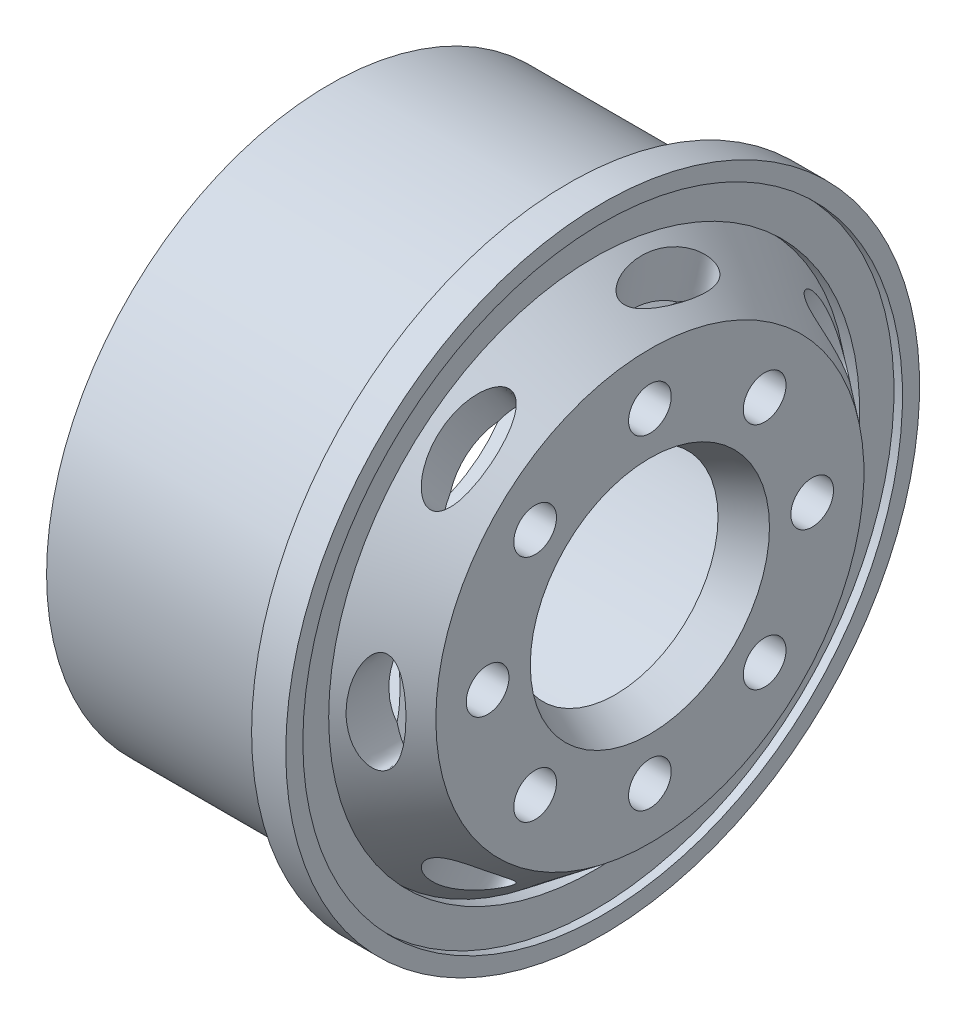
SolidWorks part; units mm, degrees
ref_plane "Front Plane" through (0, 0, 0) normal (0, 0, 1) x (1, 0, 0)
ref_plane "Top Plane" through (0, 0, 0) normal (0, 1, 0) x (1, 0, 0)
ref_plane "Right Plane" through (0, 0, 0) normal (1, 0, 0) x (0, 0, -1)
sketch "Sketch1" plane through (0, 0, 0) normal (0, 1, 0) x (1, 0, 0)
  line L0 (-37.2789, 0) -> (44.8184, 0) construction
  line L18 (5.6863, 15.538) -> (4.9553, 15.538)
  line L23 (4.9553, 15.538) -> (8.9491, 12.5285)
  line L27 (2.9431, 14.55) -> (6.9363, 11.5409)
  line L28 (4.1863, 16.55) -> (4.1863, 18.55)
  line L29 (4.1863, 18.55) -> (5.6863, 18.55)
  line L30 (5.6863, 17.55) -> (5.6863, 15.538)
  line L34 (6.9363, 11.5409) -> (6.9363, 6)
  line L37 (8.9491, 12.5285) -> (8.9491, 7)
  line L38 (6.9363, 6) -> (8.9491, 7)
  line L39 (5.6863, 18.55) -> (6.1863, 18.55)
  line L40 (6.1863, 18.55) -> (6.1863, 17.55)
  line L41 (6.1863, 17.55) -> (5.6863, 17.55)
  line L42 (4.1863, 16.55) -> (-9.8137, 16.55)
  line L43 (-9.8137, 16.55) -> (-9.8137, 14.55)
  line L44 (-9.8137, 14.55) -> (2.9431, 14.55)
  point P3 (8.936, 7.0891)
  point P4 (7.9363, 16.8502)
  point P5 (4.0798, 13.7427)
  point P16 (8.0798, 11.847)
  dimension "D2" = 12
  dimension "D4" = 14
  dimension "D5" = 2
  dimension "D6" = 1.5
  dimension "D7" = 29.1
  dimension "D8" = 3.9932
  dimension "D9" = 2
  dimension "D10" = 1
  dimension "D11" = 0.5
  dimension "D12" = 33.1
  dimension "D3" = 5
  dimension "D13" = 1.5
  dimension "D15" = 16.75
  dimension "D19" = 23.0818
  dimension "D14" = 3.2628
revolve "Revolve1" add sketch "Sketch1" angle 360 about L0
sketch "Sketch2" plane through (8.9491, 0, 0) normal (1, 0, 0) x (0, 0, -1)
  circle A0 centre (0, 0) radius 9.5 construction
  circle A1 centre (0, 9.5) radius 1.25
  circle A2 centre (6.7175, 6.7175) radius 1.25
  circle A3 centre (9.5, 0) radius 1.25
  circle A4 centre (6.7175, -6.7175) radius 1.25
  circle A5 centre (0, -9.5) radius 1.25
  circle A6 centre (-6.7175, -6.7175) radius 1.25
  circle A7 centre (-9.5, 0) radius 1.25
  circle A8 centre (-6.7175, 6.7175) radius 1.25
  point P22 (0, 0)
  dimension "D1" = 19
  dimension "D2" = 2.5
  dimension "D3" = 8
extrude "Cut-Extrude1" cut sketch "Sketch2" against normal through all
ref_plane "Plane1" through (0, 0, 15) normal (0, 0, 1) x (1, 0, 0)
sketch "Sketch3" plane through (0, 0, 15) normal (0, 0, 1) x (1, 0, 0)
  line L0 (6.9522, 14.0332) -> (6.9522, -14.0332) construction
  line L1 (8.9491, 12.5285) -> (4.9553, 15.538) construction
  line L2 (4.9553, -15.538) -> (8.9491, -12.5285) construction
  ellipse E0 centre (6.9522, 0) end of major axis (6.9522, -3) minor radius 1
  dimension "D1" = 2
  dimension "D2" = 6
extrude "Cut-Extrude2" cut sketch "Sketch3" against normal blind 3
pattern_circular "CirPattern1" count 7 over 360 about axis through (8.9491, 0, 0) along (-1, 0, 0) of "Cut-Extrude2"
